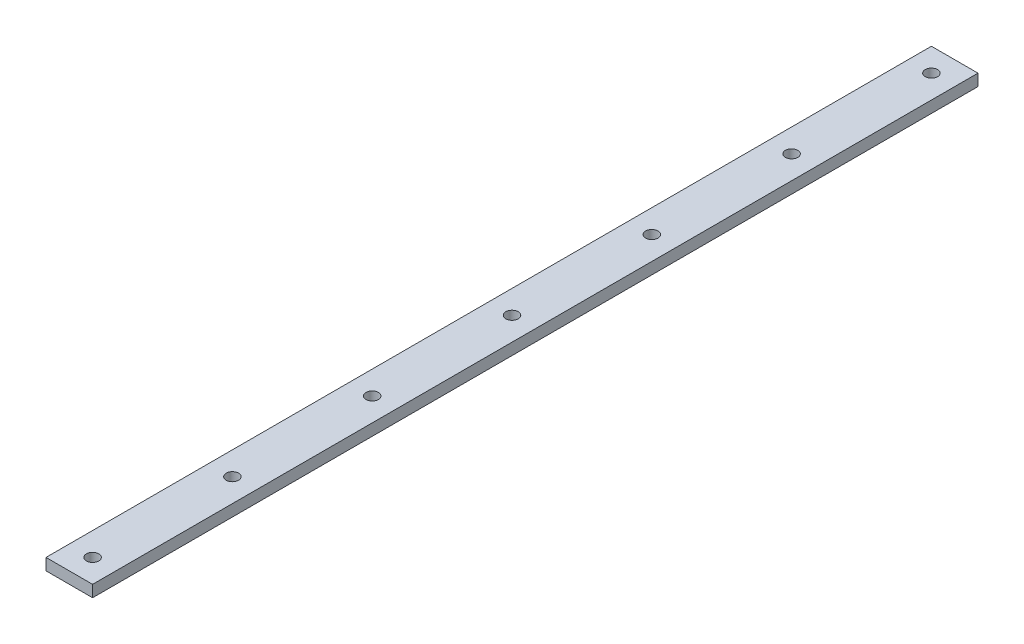
SolidWorks part; units mm, degrees
material "6061-T6 (SS)"
ref_plane "Front Plane" through (0, 0, 0) normal (0, 0, 1) x (1, 0, 0)
ref_plane "Top Plane" through (0, 0, 0) normal (0, 1, 0) x (1, 0, 0)
ref_plane "Right Plane" through (0, 0, 0) normal (1, 0, 0) x (0, 0, -1)
sketch "Sketch1" plane through (0, 0, 0) normal (0, 1, 0) x (1, 0, 0)
  line L1 (0, 0) -> (-25.4, 0)
  line L2 (0, 0) -> (0, 482.6)
  line L3 (0, 482.6) -> (-25.4, 482.6)
  line L4 (-25.4, 0) -> (-25.4, 482.6)
  dimension "D1" = 25.4
  dimension "D2" = 482.6
extrude "Boss-Extrude1" add sketch "Sketch1" along normal blind 6.35
hole_wizard "1/4 Clearance Hole1" positions "Sketch2" profile "Sketch3" hole size "1/4" standard "ANSI Inch" end condition through all
sketch "Sketch2" plane through (0, 6.35, 0) normal (0, 1, 0) x (1, 0, 0)
  line L0 (-25.4, 0) -> (0, 0) construction
  line L2 (0, 0) -> (0, 482.6) construction
  line L4 (0, 482.6) -> (-25.4, 482.6) construction
  point P0 (-12.7, 12.7)
  point P6 (-12.7, 88.9)
  point P7 (-12.7, 165.1)
  point P8 (-12.7, 241.3)
  point P9 (-12.7, 317.5)
  point P10 (-12.7, 393.7)
  point P28 (-12.7, 469.9)
  point P29 (-12.7, 559.8679)
  dimension "D2" = 12.7
  dimension "D3" = 12.7
  dimension "D4" = 12.7
  dimension "D5" = 76.2
  dimension "D1" = 7
sketch "Sketch3" plane through (-12.7, 6.35, -12.7) normal (1, 0, 0) x (0, 0, 1)
  line L0 (0, 0) -> (0, 6.35)
  line L1 (0, 6.35) -> (3.3782, 6.35)
  line L2 (3.3782, 6.35) -> (3.3782, 0)
  line L5 (3.3782, 0) -> (0, 0)
  line L11 (0, -6.35) -> (0, 107.95) construction
  dimension "Thru Hole Dia." = 6.7564
  dimension "Thru Hole Depth" = 6.35
